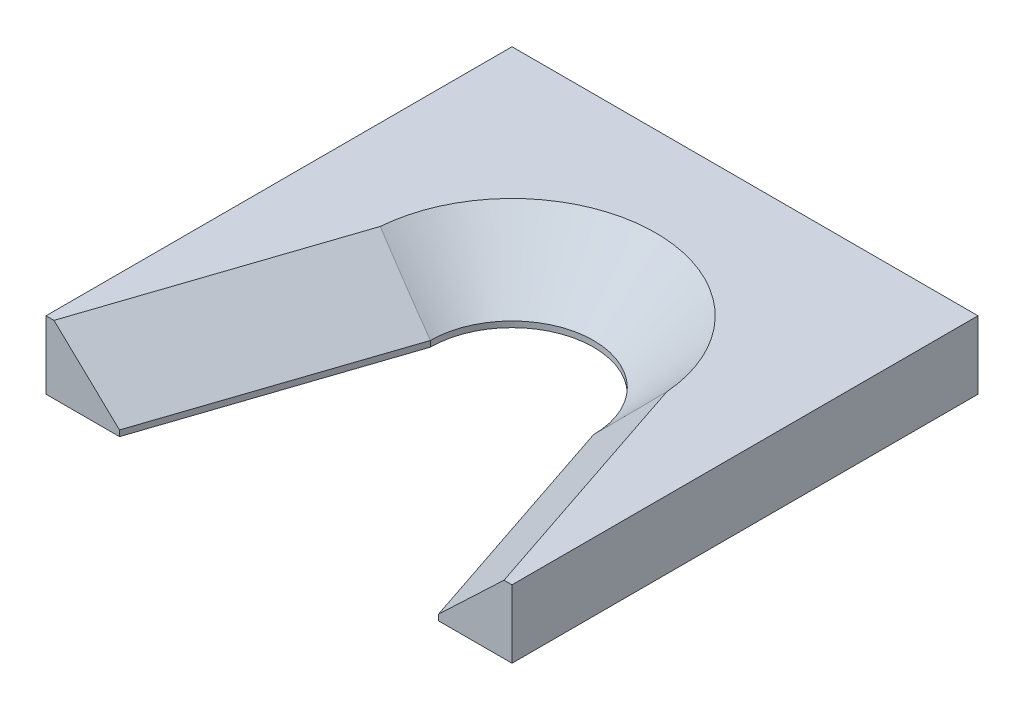
SolidWorks part; units mm, degrees
other "Markup1"
sketch "Sketch3" plane through (-63.5, 8.89, -38.1) normal (-0.9125, 0.4059, -0.0503) x (0.4069, 0.9134, -0.0121)
sketch "Sketch4" plane through (-63.5, 8.89, -38.1) normal (-0.9125, 0.4059, -0.0503) x (0.4069, 0.9134, -0.0121)
sketch "Sketch7" plane through (-63.5, 12.7, -38.1) normal (-0.9125, 0.4059, -0.0503) x (0.4069, 0.9134, -0.0121)
sketch "Sketch9" plane through (-63.5, 11.1125, -38.1) normal (-0.9125, 0.4059, -0.0503) x (0.4069, 0.9134, -0.0121)
sketch "Sketch12" plane through (-63.5, 11.1125, -38.1) normal (-0.9125, 0.4059, -0.0503) x (0.4069, 0.9134, -0.0121)
sketch "Sketch14" plane through (-38.1, 11.1125, -38.1) normal (-0.9125, 0.4059, -0.0503) x (0.4069, 0.9134, -0.0121)
sketch "Sketch16" plane through (-38.1, 11.1125, -38.1) normal (-0.9125, 0.4059, -0.0503) x (0.4069, 0.9134, -0.0121)
sketch "Sketch21" plane through (-38.1, 11.1125, -38.1) normal (-0.9125, 0.4059, -0.0503) x (0.4069, 0.9134, -0.0121)
other "Markup2"
sketch "Sketch6" plane through (-63.5, 8.89, -38.1) normal (-0.9404, 0.2221, -0.2575) x (0.2799, 0.9357, -0.215)
sketch "Sketch8" plane through (-63.5, 12.7, -38.1) normal (-0.9404, 0.2221, -0.2575) x (0.2799, 0.9357, -0.215)
sketch "Sketch10" plane through (-63.5, 11.1125, -38.1) normal (-0.9404, 0.2221, -0.2575) x (0.2799, 0.9357, -0.215)
sketch "Sketch13" plane through (-63.5, 11.1125, -38.1) normal (-0.9404, 0.2221, -0.2575) x (0.2799, 0.9357, -0.215)
sketch "Sketch15" plane through (-38.1, 11.1125, -38.1) normal (-0.9404, 0.2221, -0.2575) x (0.2799, 0.9357, -0.215)
sketch "Sketch17" plane through (-38.1, 11.1125, -38.1) normal (-0.9404, 0.2221, -0.2575) x (0.2799, 0.9357, -0.215)
sketch "Sketch22" plane through (-38.1, 11.1125, -38.1) normal (-0.9404, 0.2221, -0.2575) x (0.2799, 0.9357, -0.215)
material "1060 Alloy"
ref_plane "Front Plane" through (0, 0, 0) normal (0, 0, 1) x (1, 0, 0)
ref_plane "Top Plane" through (0, 0, 0) normal (0, 1, 0) x (1, 0, 0)
ref_plane "Right Plane" through (0, 0, 0) normal (1, 0, 0) x (0, 0, -1)
sketch "Sketch1" plane through (0, 0, 0) normal (0, 1, 0) x (1, 0, 0)
  line L0 (-13.335, 0) -> (-26.0831, -38.1)
  line L1 (38.1, 38.1) -> (-38.1, 38.1)
  line L2 (38.1, 38.1) -> (38.1, -38.1)
  line L3 (38.1, -38.1) -> (-38.1, -38.1)
  line L4 (-38.1, 38.1) -> (-38.1, -38.1)
  line L5 (38.1, 38.1) -> (-38.1, -38.1) construction
  line L6 (38.1, -38.1) -> (-38.1, 38.1) construction
  line L7 (13.335, 0) -> (26.0831, -38.1)
  circle A0 centre (0, 0) radius 13.335
  point P0 (0, 0)
  dimension "D3" = 26.67
  dimension "D1" = 76.2
  dimension "D2" = 76.2
  dimension "D4" = 37
extrude "Boss-Extrude1" add sketch "Sketch1" along normal blind 11.1125 contours A0 L7 L3 L2 L1 L4 L0
chamfer "Chamfer1" distance 10.16 angle 45 3 edges at (19.709, 11.1125, 19.05) (0, 11.1125, -13.335) (-19.709, 11.1125, 19.05)
sketch "Sketch18" plane through (0, 0, -38.1) normal (0, 0, -1) x (-1, 0, 0)
  line L0 (-38.1, 5.5562) -> (38.1, 5.5562) construction
  line L1 (-38.1, 11.1125) -> (-38.1, 0) construction
  line L2 (38.1, 11.1125) -> (38.1, 0) construction
  line L3 (0, 0) -> (0, 11.1125) construction
  line L4 (-38.1, 11.1125) -> (38.1, 11.1125) construction
  point P11 (0, 5.5562)
hole_wizard "Tap Drill for #8-32 Tap1" positions "3DSketch5" profile "Sketch20" hole size "#8-32" standard "ANSI Inch"
sketch3d "3DSketch5"
  point P0 (0, 5.5562, -38.1)
sketch "Sketch20" plane through (0, 5.5562, -38.1) normal (1, 0, 0) x (0, 1, 0)
  line L0 (0, 0) -> (0, 16.2778)
  line L1 (0, 16.2778) -> (1.7272, 15.24)
  line L2 (1.7272, 15.24) -> (1.7272, 0)
  line L5 (1.7272, 0) -> (0, 0)
  line L10 (0, 16.2778) -> (-1.7272, 15.24) construction
  line L11 (0, -6.35) -> (0, 107.95) construction
  dimension "Hole Dia." = 3.4544
  dimension "Hole Depth" = 15.24
  dimension "Drill Angle" = 118
